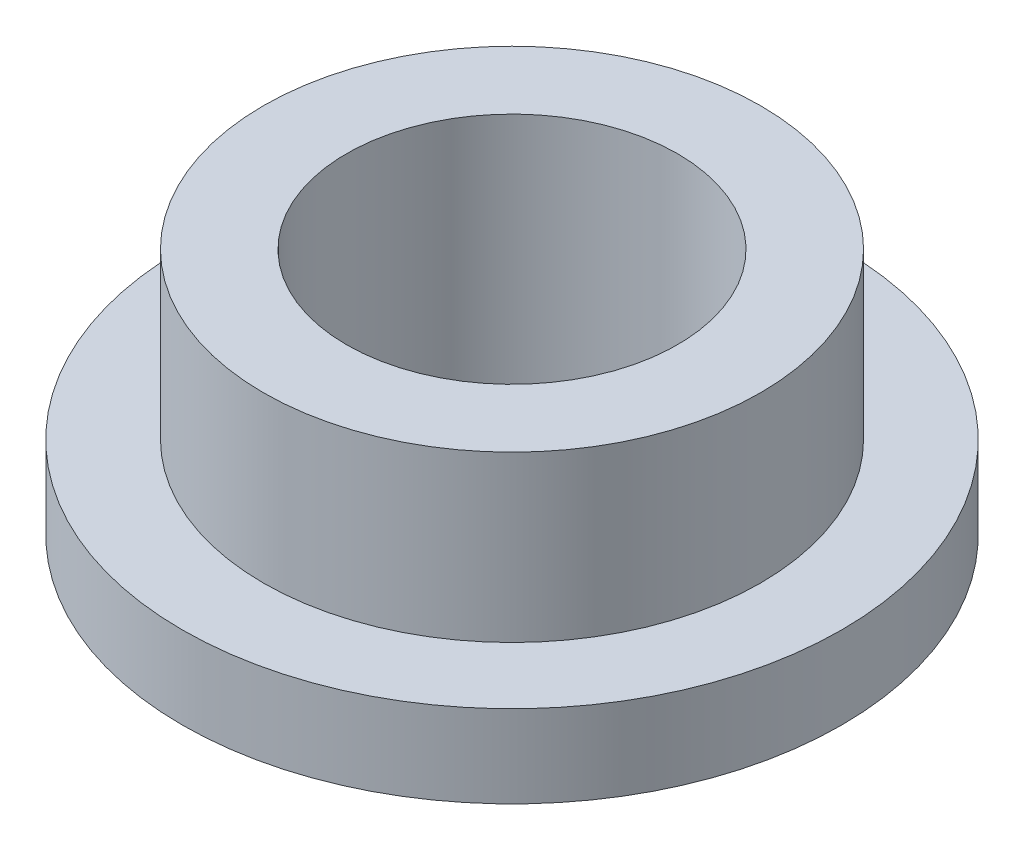
SolidWorks part; units mm, degrees
material "Aluminum Bronze"
ref_plane "Front" through (0, 0, 0) normal (0, 0, 1) x (1, 0, 0)
ref_plane "Top" through (0, 0, 0) normal (0, 1, 0) x (1, 0, 0)
ref_plane "Right" through (0, 0, 0) normal (1, 0, 0) x (0, 0, -1)
sketch "Sketch1" plane through (0, 0, 0) normal (0, 1, 0) x (1, 0, 0)
  circle A0 centre (0, 0) radius 3.1877
  circle A1 centre (0, 0) radius 4.7879
  circle A2 centre (0, 0) radius 6.35
  dimension "ID" = 6.3754
  dimension "OD" = 9.5758
  dimension "FlangeOD" = 12.7
sketch "Sketch2" plane through (0, 0, 0) normal (0, 1, 0) x (1, 0, 0)
  circle A0 centre (0, 0) radius 3.1877 construction
  circle A1 centre (0, 0) radius 4.7879 construction
  circle A2 centre (0, 0) radius 3.1877
  circle A3 centre (0, 0) radius 4.7879
extrude "Boss-Extrude1" add sketch "Sketch2" along normal blind 4.7625
sketch "Sketch3" plane through (0, 0, 0) normal (0, 1, 0) x (1, 0, 0)
  circle A0 centre (0, 0) radius 6.35 construction
  circle A1 centre (0, 0) radius 4.7879 construction
  circle A2 centre (0, 0) radius 6.35
  circle A3 centre (0, 0) radius 4.7879
extrude "Boss-Extrude2" add sketch "Sketch3" along normal blind 1.5875
